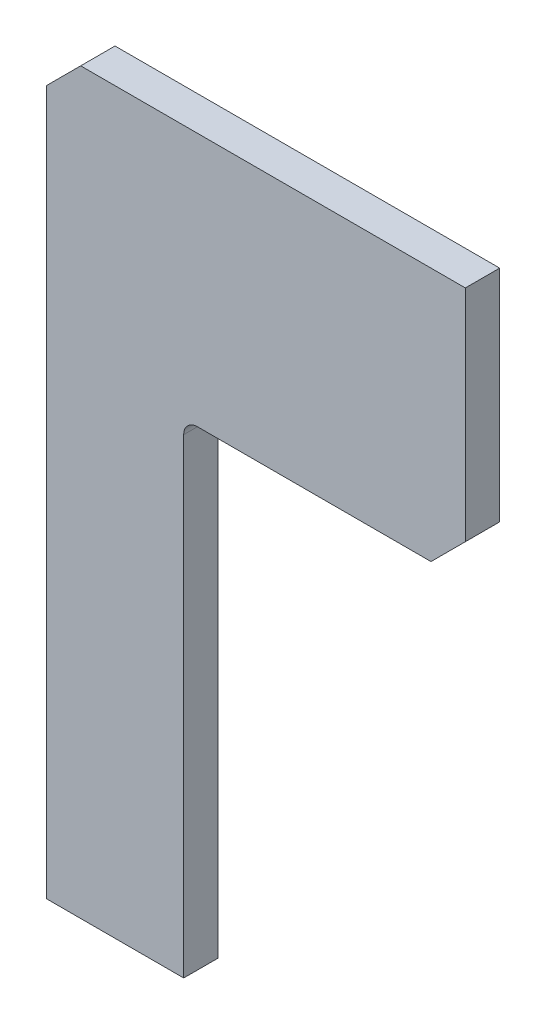
SolidWorks part; units mm, degrees
ref_plane "Front Plane" through (0, 0, 0) normal (0, 0, 1) x (1, 0, 0)
ref_plane "Top Plane" through (0, 0, 0) normal (0, 1, 0) x (1, 0, 0)
ref_plane "Right Plane" through (0, 0, 0) normal (1, 0, 0) x (0, 0, -1)
sketch "Sketch1" plane through (0, 0, 0) normal (0, 0, 1) x (1, 0, 0)
  line L0 (0, 0) -> (0, 205)
  line L1 (10, 215) -> (122, 215)
  line L2 (122, 215) -> (122, 151)
  line L3 (112, 141) -> (44, 141)
  line L4 (40, 137) -> (40, 0)
  line L5 (40, 0) -> (0, 0)
  line L6 (0, 205) -> (10, 215)
  line L7 (122, 151) -> (112, 141)
  arc A0 (44, 141) -> (40, 137) centre (44, 137) ccw
  point P1 (0, 215)
  point P5 (122, 141)
  dimension "D1" = 4
  dimension "D2" = 215
  dimension "D3" = 122
  dimension "D4" = 40
  dimension "D5" = 74
extrude "Boss-Extrude1" add sketch "Sketch1" along normal blind 10
